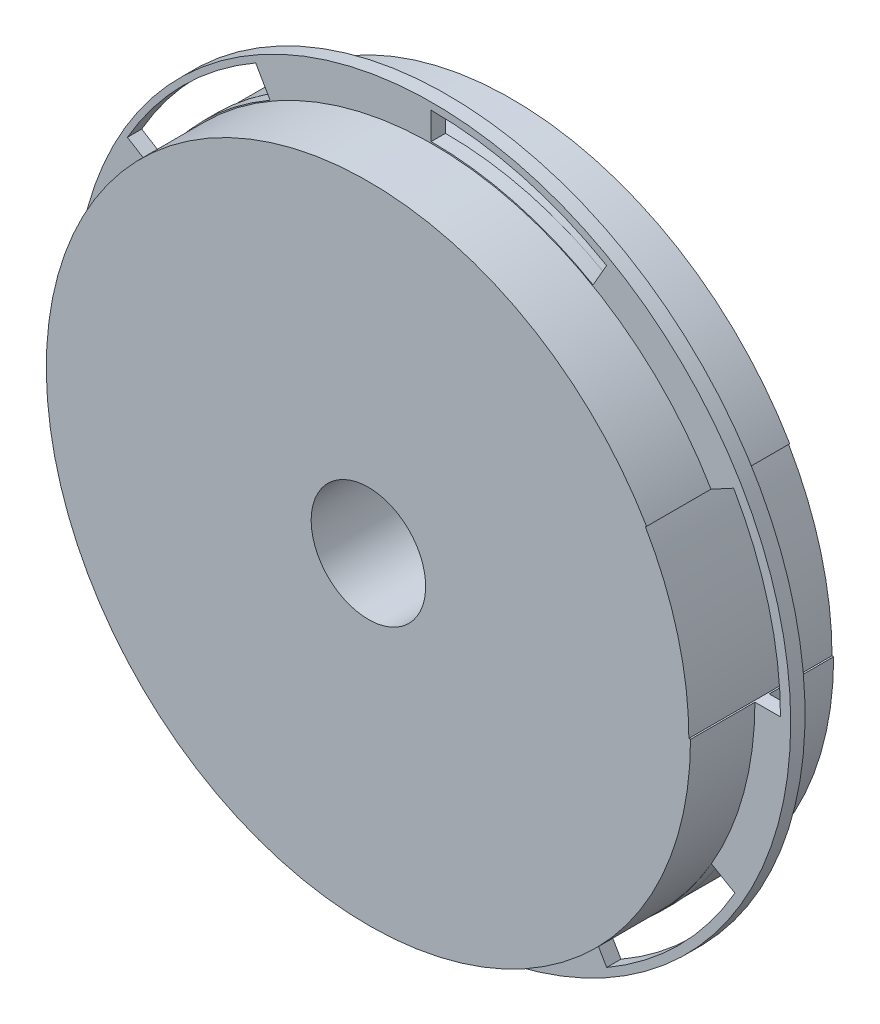
SolidWorks part; units mm, degrees
ref_plane "Front Plane" through (0, 0, 0) normal (0, 0, 1) x (1, 0, 0)
ref_plane "Top Plane" through (0, 0, 0) normal (0, 1, 0) x (1, 0, 0)
ref_plane "Right Plane" through (0, 0, 0) normal (1, 0, 0) x (0, 0, -1)
sketch "Sketch1" plane through (0, 0, 0) normal (0, 0, 1) x (1, 0, 0)
  circle A0 centre (-23.5895, 15.6012) radius 25
  dimension "D1" = 50
extrude "Boss-Extrude1" add sketch "Sketch1" along normal blind 10
sketch "Sketch2" plane through (0, 0, 10) normal (0, 0, 1) x (1, 0, 0)
  line L0 (-1.2044, 15.599) -> (0.6956, 15.6012)
  line L1 (-4.2478, 26.8991) -> (-2.5745, 27.8009)
  line L2 (-23.703, 15.6) -> (-3.4347, 50.7057) construction
  line L3 (-4.1329, 4.3012) -> (-2.4875, 3.3512)
  line L4 (-12.3974, -3.9845) -> (-11.4474, -5.63)
  line L5 (-23.7052, -6.9989) -> (-23.7052, -8.8989)
  line L6 (-35.0131, -3.9845) -> (-35.9631, -5.63)
  line L7 (-43.1556, 4.2945) -> (-44.923, 3.3512)
  line L8 (-46.199, 15.5945) -> (-48.2209, 15.6012)
  line L9 (-43.2206, 26.7971) -> (-44.923, 27.8513)
  line L10 (-34.9562, 35.0828) -> (-35.9631, 36.8325)
  line L11 (-23.7052, 38.2014) -> (-23.7052, 40.1014)
  line L12 (-12.3974, 35.187) -> (-11.4474, 36.8325)
  circle A2 centre (-23.6879, 15.4641) radius 5.8533
  arc A3 (-11.4474, -5.63) -> (-2.4875, 3.3512) centre (-23.6474, 15.501) ccw
  circle A4 centre (-23.6879, 15.4641) radius 13.2254
  arc A5 (0.6956, 15.6012) -> (-2.5745, 27.8009) centre (-23.7044, 15.599) ccw
  arc A6 (-1.2044, 15.599) -> (-4.2478, 26.8991) centre (-23.7044, 15.599) ccw
  arc A7 (-12.3974, -3.9845) -> (-4.1329, 4.3012) centre (-23.6474, 15.501) ccw
  circle A8 centre (-23.6879, 15.4641) radius 14.99
  arc A9 (-35.9631, -5.63) -> (-23.7052, -8.8989) centre (-23.7631, 15.501) ccw
  arc A10 (-35.0131, -3.9845) -> (-23.7052, -6.9989) centre (-23.7631, 15.501) ccw
  circle A11 centre (-23.7053, 15.5954) radius 14.99
  arc A12 (-48.2209, 15.6012) -> (-44.923, 3.3512) centre (-23.8209, 15.6012) ccw
  arc A13 (-46.199, 15.5945) -> (-43.1556, 4.2945) centre (-23.699, 15.5945) ccw
  circle A14 centre (-23.7062, 15.599) radius 14.99
  arc A15 (-35.9631, 36.8325) -> (-44.923, 27.8513) centre (-23.7631, 15.7015) ccw
  arc A16 (-34.9562, 35.0828) -> (-43.2206, 26.7971) centre (-23.7062, 15.5972) ccw
  circle A17 centre (-23.7062, 15.5972) radius 14.99
  arc A18 (-11.4474, 36.8325) -> (-23.7052, 40.1014) centre (-23.6474, 15.7015) ccw
  arc A19 (-12.3974, 35.187) -> (-23.7052, 38.2014) centre (-23.6474, 15.7015) ccw
  circle A20 centre (-23.6474, 15.7015) radius 14.99
  point P54 (-23.7052, 15.6012)
  dimension "D3" = 0
extrude "Cut-Extrude5" cut sketch "Sketch2" against normal blind 10 contours A19 L12 A18 L11 | A13 L8 A12 L7 | A16 L10 A15 L9 | A5 L1 A6 L0 | A7 L3 A3 L4 | A10 L5 A9 L6
sketch "Sketch3" plane through (0, 0, 0) normal (0, 0, -1) x (-1, 0, 0)
  circle A0 centre (23.5895, 15.6012) radius 4
  circle A1 centre (23.5895, 15.6012) radius 25 construction
  dimension "D1" = 0
  dimension "D2" = 8
extrude "Cut-Extrude6" cut sketch "Sketch3" against normal through all
sketch "Sketch4" plane through (0, 0, 10) normal (0, 0, 1) x (1, 0, 0)
  circle A0 centre (-23.5895, 15.6012) radius 25
  circle A1 centre (-23.5895, 15.6012) radius 25 construction
  circle A2 centre (-23.5895, 15.6012) radius 22.5
  dimension "D1" = 50
  dimension "D2" = 0
  dimension "D3" = 45
  dimension "D4" = 0
extrude "Cut-Extrude7" cut sketch "Sketch4" against normal blind 4.5
sketch "Sketch5" plane through (0, 0, 0) normal (0, 0, -1) x (-1, 0, 0)
  circle A0 centre (23.5895, 15.6012) radius 25
  circle A1 centre (23.5895, 15.6012) radius 25 construction
  circle A2 centre (23.5895, 15.6012) radius 22.5
  dimension "D1" = 50
  dimension "D2" = 0
  dimension "D3" = 45
  dimension "D4" = 0
extrude "Cut-Extrude8" cut sketch "Sketch5" against normal blind 4.5
